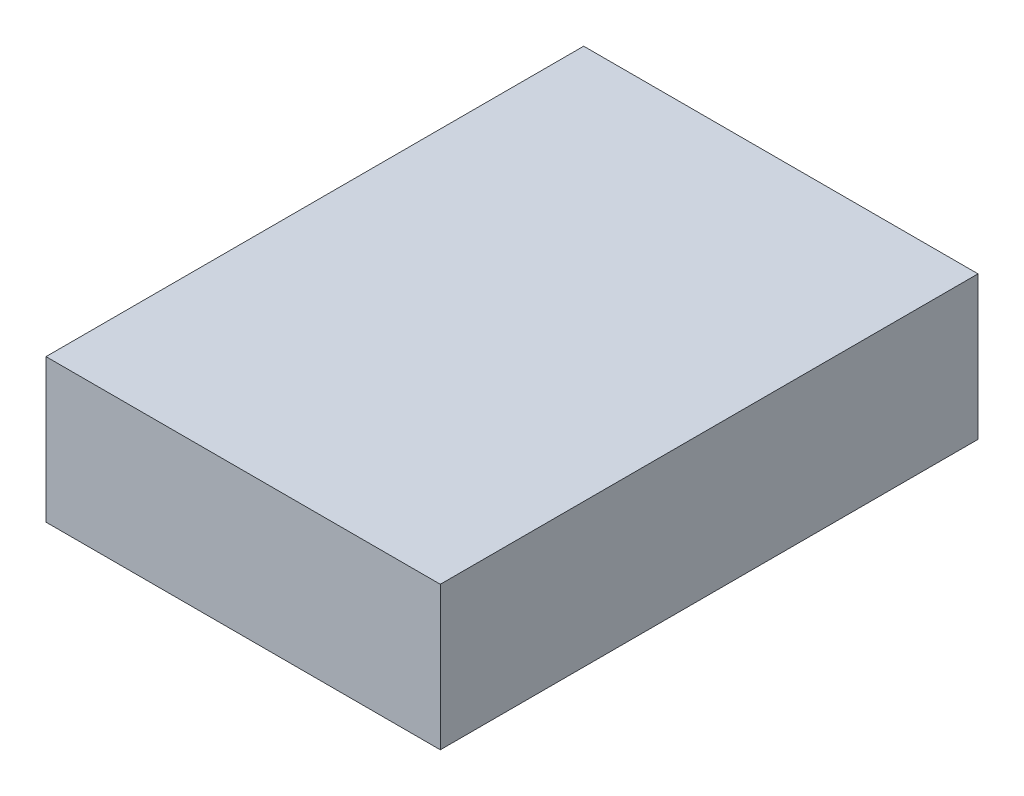
SolidWorks part; units mm, degrees
ref_plane "Front Plane" through (0, 0, 0) normal (0, 0, 1) x (1, 0, 0)
ref_plane "Top Plane" through (0, 0, 0) normal (0, 1, 0) x (1, 0, 0)
ref_plane "Right Plane" through (0, 0, 0) normal (1, 0, 0) x (0, 0, -1)
sketch "Sketch1" plane through (0, 0, 0) normal (0, 1, 0) x (1, 0, 0)
  line L1 (0, 0) -> (69.85, 0)
  line L2 (0, 0) -> (0, 95.25)
  line L3 (0, 95.25) -> (69.85, 95.25)
  line L4 (69.85, 0) -> (69.85, 95.25)
  dimension "D1" = 69.85
  dimension "D2" = 95.25
extrude "Boss-Extrude1" add sketch "Sketch1" along normal blind 25.4
